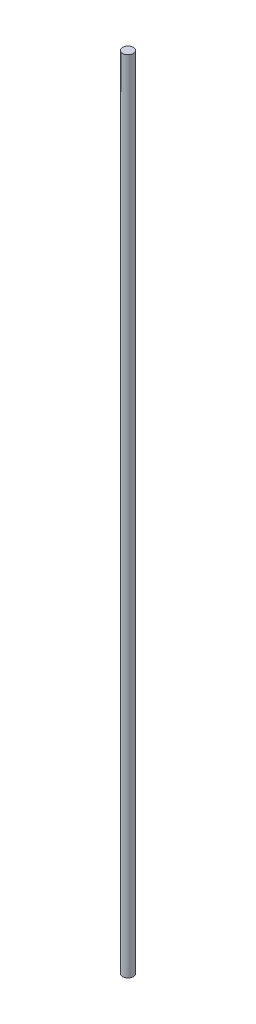
SolidWorks part; units mm, degrees
ref_plane "Front Plane" through (0, 0, 0) normal (0, 0, 1) x (1, 0, 0)
ref_plane "Top Plane" through (0, 0, 0) normal (0, 1, 0) x (1, 0, 0)
ref_plane "Right Plane" through (0, 0, 0) normal (1, 0, 0) x (0, 0, -1)
sketch "Sketch1" plane through (0, 0, 0) normal (0, 1, 0) x (1, 0, 0)
  circle A0 centre (0, 0) radius 3.175
  dimension "D1" = 6.35
extrude "Boss-Extrude1" add sketch "Sketch1" along normal blind 475
